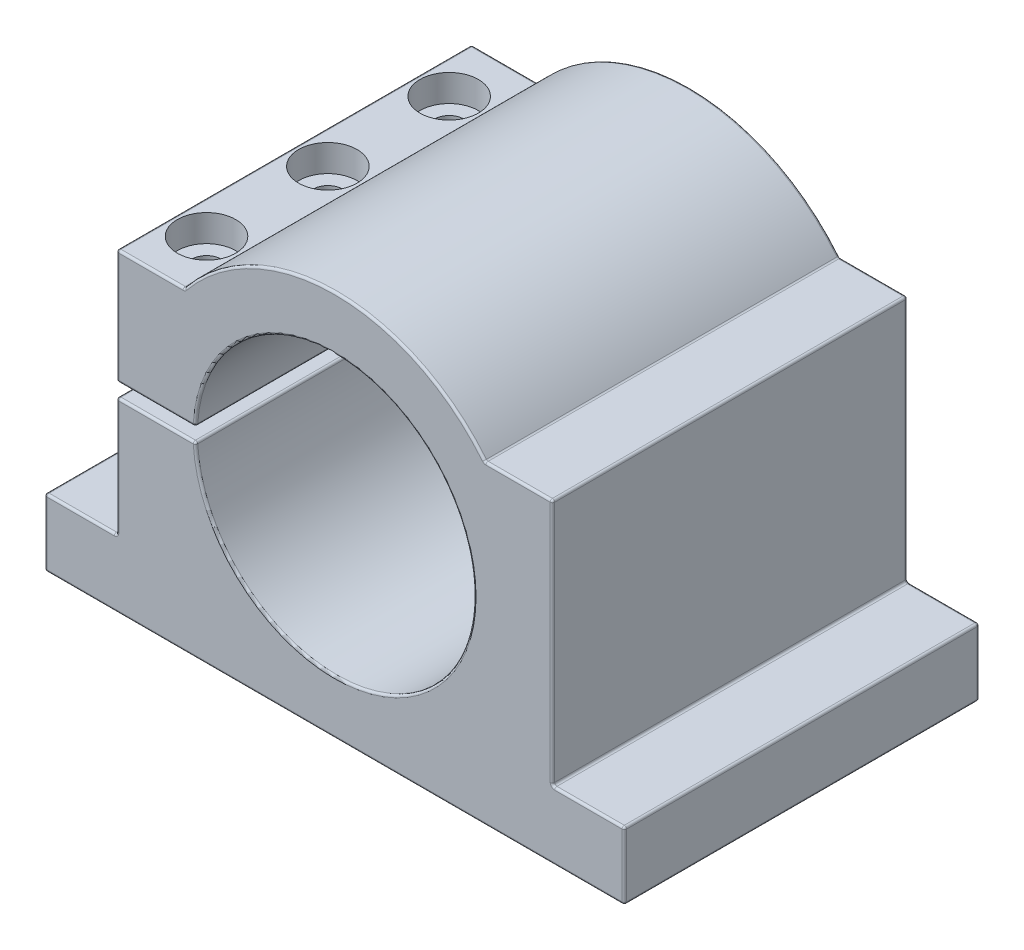
SolidWorks part; units mm, degrees
ref_plane "Спереди" through (0, 0, 0) normal (0, 0, 1) x (1, 0, 0)
ref_plane "Сверху" through (0, 0, 0) normal (0, 1, 0) x (1, 0, 0)
ref_plane "Справа" through (0, 0, 0) normal (1, 0, 0) x (0, 0, -1)
sketch "Эскиз1" plane through (0, 0, 0) normal (0, 0, 1) x (1, 0, 0)
  line L0 (0, 0) -> (0, -43) construction
  line L1 (0, -43) -> (-64.5, -43) construction
  line L2 (64.5, -43) -> (-64.5, -43)
  line L3 (-64.5, -43) -> (-64.5, -28)
  line L4 (-64.5, -28) -> (-48.5, -28)
  line L5 (-48.5, -28) -> (-48.5, 27)
  line L6 (-48.5, 27) -> (-33.4664, 27)
  line L7 (149.6575, 386.7446) -> (1009.6575, 386.7446) construction
  line L8 (0, 1.5) -> (-48.5, 1.5)
  line L9 (0, 1.5) -> (0, -1.5)
  line L10 (0, -1.5) -> (-48.5, -1.5)
  line L11 (-48.5, 1.5) -> (-48.5, -1.5)
  line L12 (48.5, 27) -> (33.4664, 27)
  line L13 (48.5, -28) -> (48.5, 27)
  line L14 (64.5, -28) -> (48.5, -28)
  line L15 (64.5, -43) -> (64.5, -28)
  circle A0 centre (0, 0) radius 31
  circle A1 centre (0, 0) radius 43
  point P11 (0, 43)
  point P15 (0, 0)
  dimension "D1" = 62
  dimension "D2" = 129
  dimension "D3" = 43
  dimension "D4" = 86
  dimension "D5" = 15
  dimension "D6" = 16
  dimension "D7" = 70
  dimension "D8" = 3
extrude "Бобышка-Вытянуть1" add sketch "Эскиз1" along normal mid plane 79 contours A1 L10 L5 L4 L3 L2 | A1 L6 L5 L8 | A1 L8 A0 L10 | A1 L2 L15 L14 L13 L12
sketch "Эскиз2" plane through (0, 27, 0) normal (0, 1, 0) x (1, 0, 0)
  line L0 (-40.9832, 39.5) -> (-40.9832, -39.5) construction
  line L1 (-48.5, 39.5) -> (-33.4664, 39.5) construction
  line L2 (-48.5, -39.5) -> (-33.4664, -39.5) construction
  circle A0 centre (-40.9832, 27) radius 6.5
  circle A1 centre (-40.9832, 0) radius 6.5
  circle A2 centre (-40.9832, -27) radius 6.5
  dimension "D1" = 13
  dimension "D2" = 27
  dimension "D3" = 27
extrude "Вырез-Вытянуть1" cut sketch "Эскиз2" against normal blind 6
sketch "Эскиз3" plane through (0, 21, 0) normal (0, 1, 0) x (1, 0, 0)
  circle A0 centre (-40.9832, 27) radius 3.25
  circle A1 centre (-40.9832, 0) radius 3.25
  circle A2 centre (-40.9832, -27) radius 3.25
  dimension "D1" = 6.5
extrude "Вырез-Вытянуть2" cut sketch "Эскиз3" against normal up to surface (22.5 mm away) up to face at (-39.7318, -1.5, 0)
sketch "Эскиз4" plane through (0, -1.5, 0) normal (0, 1, 0) x (1, 0, 0)
  circle A0 centre (-40.9832, 27) radius 2.6
  circle A1 centre (-40.9832, 0) radius 2.6
  circle A2 centre (-40.9832, -27) radius 2.6
  dimension "D1" = 5.2
extrude "Вырез-Вытянуть3" cut sketch "Эскиз4" against normal blind 30
fillet "Скругление1" radius 0.5 42 edges at (48.5, -28, 0) (48.5, 27, 0) (64.5, -43, 0) (64.5, -28, 0) (-64.5, -28, 0) (-64.5, -43, 0) (-48.5, -1.5, 0) (-48.5, -28, 0) (-48.5, 27, 0) (-48.5, 1.5, 0) (33.4664, 27, 0) (-33.4664, 27, 0) (64.5, -35.5, -39.5) (56.5, -28, -39.5) (48.5, -0.5, -39.5) (40.9832, 27, -39.5) (0, 43, -39.5) (-40.9832, 27, -39.5) (-48.5, 14.25, -39.5) (-39.7318, 1.5, -39.5) (-39.7318, -1.5, -39.5) (-48.5, -14.75, -39.5) (-56.5, -28, -39.5) (-64.5, -35.5, -39.5) (0, -43, -39.5) (-30.9637, 1.5, 0) (-30.9637, -1.5, 0) (31, 0, -39.5) (-64.5, -35.5, 39.5) (-56.5, -28, 39.5) (-48.5, -14.75, 39.5) (-39.7318, -1.5, 39.5) (31, 0, 39.5) (-39.7318, 1.5, 39.5) (-48.5, 14.25, 39.5) (-40.9832, 27, 39.5) (0, 43, 39.5) (40.9832, 27, 39.5) (48.5, -0.5, 39.5) (56.5, -28, 39.5) (64.5, -35.5, 39.5) (0, -43, 39.5)
